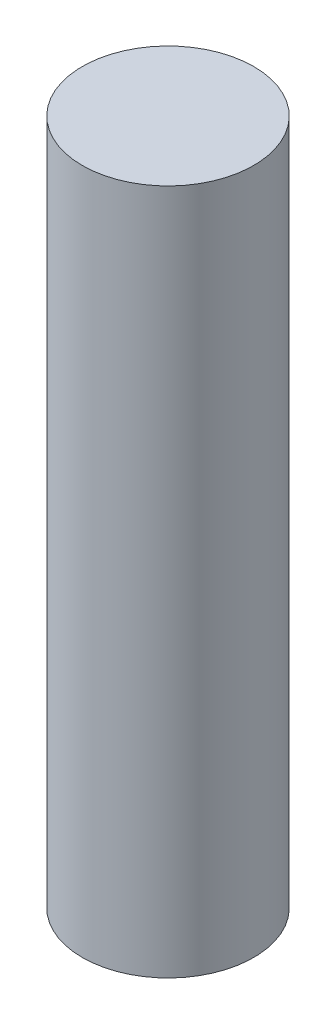
SolidWorks part; units mm, degrees
ref_plane "Front Plane" through (0, 0, 0) normal (0, 0, 1) x (1, 0, 0)
ref_plane "Top Plane" through (0, 0, 0) normal (0, 1, 0) x (1, 0, 0)
ref_plane "Right Plane" through (0, 0, 0) normal (1, 0, 0) x (0, 0, -1)
sketch "Sketch1" plane through (0, 0, 0) normal (0, 1, 0) x (1, 0, 0)
  circle A0 centre (0, 0) radius 6.35
extrude "Boss-Extrude1" add sketch "Sketch1" along normal blind 50.8 contours A0
